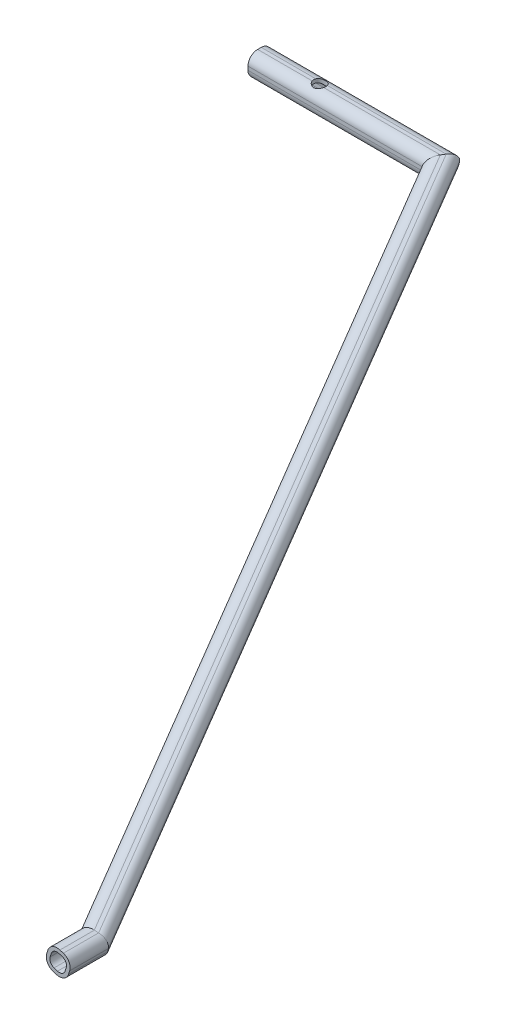
SolidWorks part; units mm, degrees
ref_plane "Front Plane" through (0, 0, 0) normal (0, 0, 1) x (1, 0, 0)
ref_plane "Top Plane" through (0, 0, 0) normal (0, 1, 0) x (1, 0, 0)
ref_plane "Right Plane" through (0, 0, 0) normal (1, 0, 0) x (0, 0, -1)
sketch "Sketch2" plane through (0, 0, 0) normal (1, 0, 0) x (0, 0, -1)
  line L1 (-1.5, -6.5) -> (1.5, -6.5)
  line L2 (-6.5, -1.5) -> (-6.5, 1.5)
  line L3 (-1.5, 6.5) -> (1.5, 6.5)
  line L4 (6.5, -1.5) -> (6.5, 1.5)
  line L5 (-6.5, -6.5) -> (6.5, 6.5) construction
  line L6 (-6.5, 6.5) -> (6.5, -6.5) construction
  arc A0 (6.5, -1.5) -> (1.5, -6.5) centre (1.5, -1.5) cw
  arc A1 (-1.5, -6.5) -> (-6.5, -1.5) centre (-1.5, -1.5) cw
  arc A2 (-6.5, 1.5) -> (-1.5, 6.5) centre (-1.5, 1.5) cw
  arc A3 (1.5, 6.5) -> (6.5, 1.5) centre (1.5, 1.5) cw
  point P0 (0, 0)
  dimension "D3" = 5
  dimension "D1" = 13
  dimension "D2" = 13
sketch3d "3DSketch2"
  line L0 (0, 0, 0) -> (363.1699, 0, 0) construction
  line L1 (363.1699, 0, 0) -> (363.1699, -200, 0) construction
  line L2 (363.1699, -200, 0) -> (363.1699, -200, 500) construction
  line L3 (0, 0, 0) -> (150, 0, 0)
  line L4 (150, 0, 0) -> (363.1699, -200, 500)
  line L5 (363.1699, -200, 500) -> (363.1699, -200, 530)
  line L6 (0, 0, 0) -> (0, -210, 0) construction
  dimension "D1" = 150
  dimension "D2" = 30
  dimension "D3" = 200
  dimension "D4" = 500
  dimension "D5" = 210
sweep "Sweep-Thin3" add profiles "Sketch2" path "3DSketch2" parameters "D1"=3
sketch "Sketch21" plane through (0, 0, 0) normal (0, 1, 0) x (1, 0, 0)
  line L0 (0, 0) -> (150, 0) construction
  circle A0 centre (50, 0) radius 5
  dimension "D1" = 10
  dimension "D2" = 50
extrude "Cut-Extrude3" cut sketch "Sketch21" against normal through all both and the other way through all
sketch "Sketch22" [suppressed] plane through (0, 0, 0) normal (0, 0, 1) x (1, 0, 0)
ref_plane "Plane1" [suppressed] through (0, -210, 0) normal (0, 1, 0) x (1, 0, 0)
ref_plane "Plane2" through (0, -210, 0) normal (0, -1, 0) x (-1, 0, 0)
